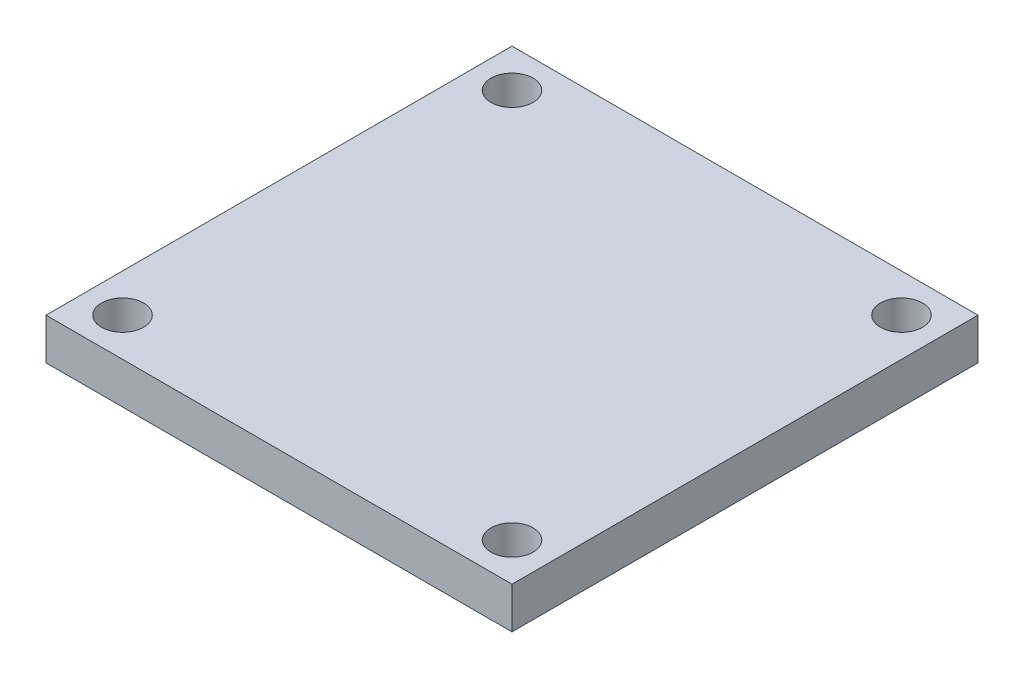
SolidWorks part; units mm, degrees
ref_plane "Front Plane" through (0, 0, 0) normal (0, 0, 1) x (1, 0, 0)
ref_plane "Top Plane" through (0, 0, 0) normal (0, 1, 0) x (1, 0, 0)
ref_plane "Right Plane" through (0, 0, 0) normal (1, 0, 0) x (0, 0, -1)
sketch "Sketch1" plane through (0, 0, 0) normal (0, 1, 0) x (1, 0, 0)
  line L0 (-23.57, 0) -> (23.57, 0) construction
  line L1 (-28.2, -28.2) -> (28.2, -28.2)
  line L2 (-28.2, -28.2) -> (-28.2, 28.2)
  line L3 (-28.2, 28.2) -> (28.2, 28.2)
  line L4 (28.2, -28.2) -> (28.2, 28.2)
  line L5 (-28.2, -28.2) -> (28.2, 28.2) construction
  line L6 (-28.2, 28.2) -> (28.2, -28.2) construction
  line L7 (-23.57, -28.2) -> (-23.57, -23.57) construction
  line L8 (-23.57, -23.57) -> (-28.2, -23.57) construction
  line L9 (0, -28.2) -> (0, 28.2) construction
  circle A0 centre (-23.57, -23.57) radius 2.55
  circle A1 centre (23.57, -23.57) radius 2.55
  circle A2 centre (23.57, 23.57) radius 2.55
  circle A3 centre (-23.57, 23.57) radius 2.55
  point P0 (0, 0)
  point P9 (0, 0)
  dimension "D3" = 5.1
  dimension "D1" = 56.4
  dimension "D2" = 47.14
extrude "Boss-Extrude1" add sketch "Sketch1" along normal blind 5
